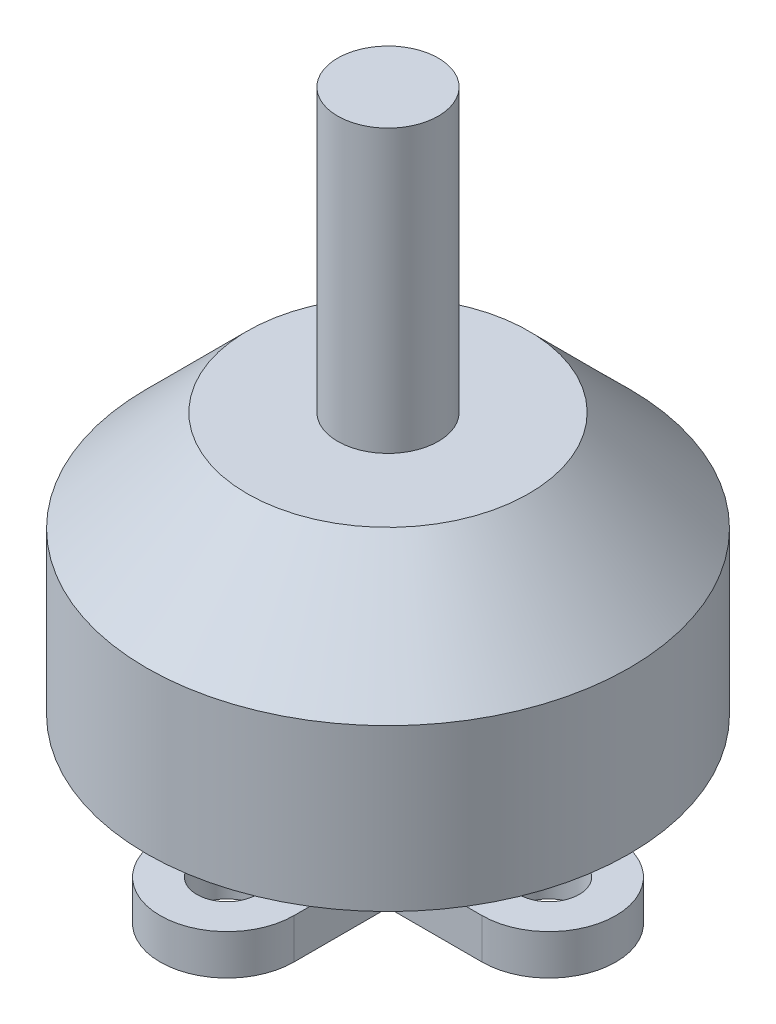
SolidWorks part; units mm, degrees
ref_plane "前视基准面" through (0, 0, 0) normal (0, 0, 1) x (1, 0, 0)
ref_plane "上视基准面" through (0, 0, 0) normal (0, 1, 0) x (1, 0, 0)
ref_plane "右视基准面" through (0, 0, 0) normal (1, 0, 0) x (0, 0, -1)
sketch "草图1" plane through (0, 0, 0) normal (0, 1, 0) x (1, 0, 0)
  line L0 (0, -8) -> (0, -6.5) construction
  line L1 (-3.3202, -8) -> (-3.3202, -4.3202)
  line L2 (3.3202, -8) -> (3.3202, -4.3202)
  line L3 (-8, 0) -> (3.3202, 0) construction
  line L4 (-8, 3.3202) -> (-4.3202, 3.3202)
  line L5 (-8, -3.3202) -> (-4.3202, -3.3202)
  line L6 (0, 8) -> (0, 3.3202) construction
  line L7 (3.3202, 8) -> (3.3202, 4.3202)
  line L8 (-3.3202, 8) -> (-3.3202, 4.3202)
  line L9 (8, 0) -> (6.5, 0) construction
  line L10 (8, -3.3202) -> (4.3202, -3.3202)
  line L11 (8, 3.3202) -> (4.3202, 3.3202)
  line L15 (3.3202, 3.3202) -> (8, 3.3202)
  line L19 (-3.3202, 3.3202) -> (-8, 3.3202)
  line L20 (-3.3202, 3.3202) -> (-3.3202, 8)
  line L21 (-3.3202, -3.3202) -> (-3.3202, -8)
  line L22 (0, 3.3202) -> (0, 8) construction
  line L23 (0, -6.5) -> (0, -8) construction
  line L24 (3.3202, 3.3202) -> (3.3202, 8)
  line L25 (3.3202, -3.3202) -> (3.3202, -8)
  line L26 (3.3202, 0) -> (-8, 0) construction
  line L27 (6.5, 0) -> (8, 0) construction
  line L28 (-3.3202, -3.3202) -> (-8, -3.3202)
  line L29 (3.3202, -3.3202) -> (8, -3.3202)
  circle A0 centre (0, 0) radius 8 construction
  circle A1 centre (-8, 0) radius 1.5
  circle A2 centre (0, 8) radius 1.5
  circle A3 centre (8, 0) radius 1.5
  circle A4 centre (0, -8) radius 1.5
  arc A5 (-3.3202, -8) -> (3.3202, -8) centre (0, -8) ccw
  arc A6 (3.3202, 8) -> (-3.3202, 8) centre (0, 8) ccw
  arc A7 (-8, 3.3202) -> (-8, -3.3202) centre (-8, 0) ccw
  arc A8 (8, -3.3202) -> (8, 3.3202) centre (8, 0) ccw
  arc A9 (3.3202, 8) -> (-3.3202, 8) centre (0, 8) ccw
  arc A10 (-3.3202, -8) -> (3.3202, -8) centre (0, -8) ccw
  arc A11 (8, -3.3202) -> (8, 3.3202) centre (8, 0) ccw
  arc A12 (-8, 3.3202) -> (-8, -3.3202) centre (-8, 0) ccw
  arc A17 (-3.3202, -4.3202) -> (-4.3202, -3.3202) centre (-4.3202, -4.3202) ccw
  arc A18 (3.3202, -4.3202) -> (4.3202, -3.3202) centre (4.3202, -4.3202) cw
  arc A19 (4.3202, 3.3202) -> (3.3202, 4.3202) centre (4.3202, 4.3202) cw
  arc A20 (-4.3202, 3.3202) -> (-3.3202, 4.3202) centre (-4.3202, 4.3202) ccw
  point P5 (0, 0)
  point P14 (0, 0)
  point P19 (0, 0)
  point P20 (0, 0)
  point P27 (0, 0)
  point P34 (0, 0)
  point P41 (0, 0)
  point P50 (0, 0)
  dimension "D1" = 16
  dimension "D2" = 3
  dimension "D4" = 1
  dimension "D3" = 4
extrude "凸台-拉伸1" add sketch "草图1" along normal blind 2 contours L10 A8 L11 L15 L24 L7 A6 L8 L20 L19 L4 A7 L5 L28 L21 L1 A5 L2 L25 L29 A1 A2 A3 A4
sketch "草图2" plane through (0, 2, 0) normal (0, 1, 0) x (1, 0, 0)
  circle A0 centre (0, 0) radius 4.6955
extrude "凸台-拉伸2" add sketch "草图2" along normal blind 3
sketch "草图3" plane through (0, 5, 0) normal (0, 1, 0) x (1, 0, 0)
  circle A0 centre (0, 0) radius 12
  dimension "D1" = 24
extrude "凸台-拉伸3" add sketch "草图3" along normal blind 13
chamfer "倒角1" distance 5 angle 45 1 edges at (0, 18, 12)
sketch "草图4" plane through (0, 18, 0) normal (0, 1, 0) x (1, 0, 0)
  circle A0 centre (0, 0) radius 2.5
  dimension "D1" = 5
extrude "凸台-拉伸4" add sketch "草图4" along normal blind 14
